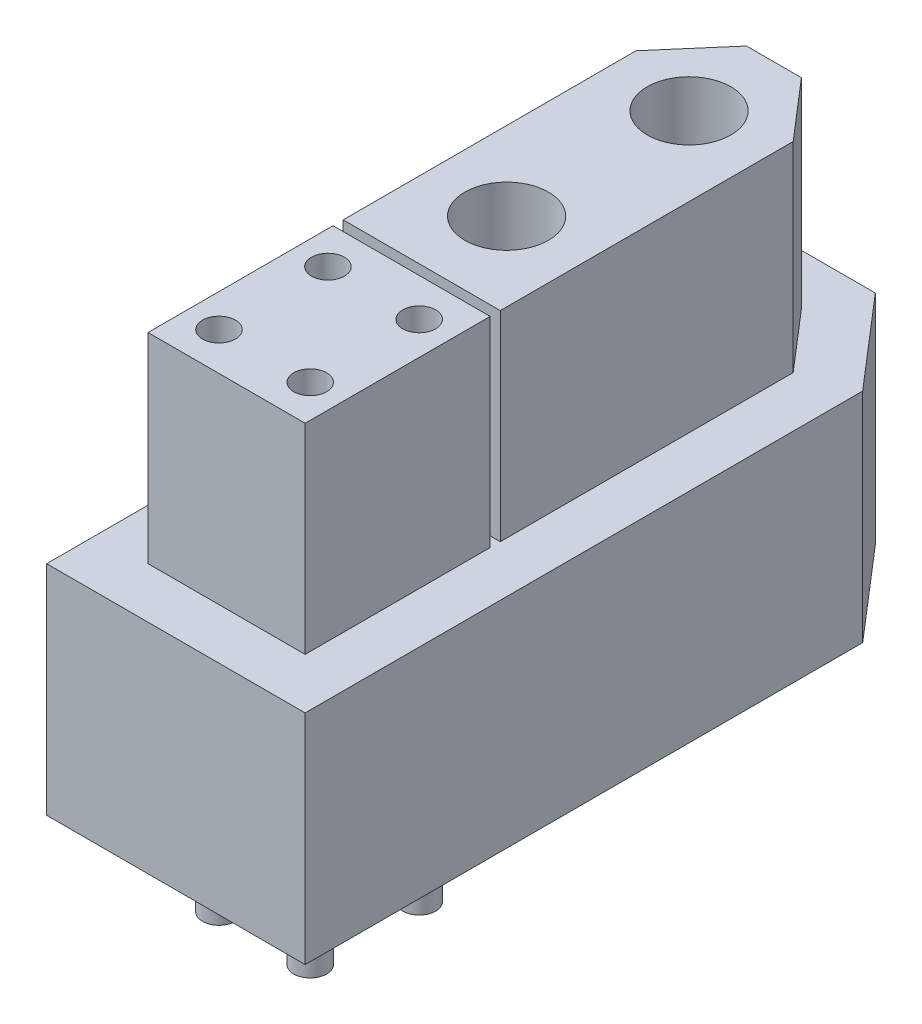
SolidWorks part; units mm, degrees
ref_plane "前视基准面" through (0, 0, 0) normal (0, 0, 1) x (1, 0, 0)
ref_plane "上视基准面" through (0, 0, 0) normal (0, 1, 0) x (1, 0, 0)
ref_plane "右视基准面" through (0, 0, 0) normal (1, 0, 0) x (0, 0, -1)
sketch "草图1" plane through (0, 0, 0) normal (0, 1, 0) x (1, 0, 0)
  line L0 (0, 0) -> (0, 22)
  line L1 (0, 22) -> (3.1, 25.6)
  line L2 (3.1, 25.6) -> (7.1, 25.6)
  line L3 (0, 0) -> (10.2, 0)
  line L4 (5.1, 0) -> (5.1, 25.6) construction
  line L5 (10.2, 22) -> (7.1, 25.6)
  line L6 (10.2, 0) -> (10.2, 22)
  point P3 (2.8038, 20.2062)
  dimension "D1" = 10.2
  dimension "D2" = 25.6
  dimension "D3" = 3.6
  dimension "D4" = 4
extrude "凸台-拉伸1" add sketch "草图1" along normal blind 8.6
sketch "草图2" plane through (0, 8.6, 0) normal (0, 1, 0) x (1, 0, 0)
  line L0 (6.1829, 23.6) -> (6.1829, 9.7) construction
  line L1 (6.1829, 16.65) -> (2.9178, 16.65) construction
  line L2 (8.2, 5.65) -> (2, 5.65) construction
  line L6 (2, 9.7) -> (8.2, 9.7)
  line L7 (2, 9.3) -> (8.2, 9.3)
  line L8 (2, 9.3) -> (2, 2)
  line L9 (8.2, 9.7) -> (8.2, 21.2576)
  line L10 (5.1, 2) -> (5.1, 23.6) construction
  line L12 (2, 2) -> (8.2, 2)
  line L13 (8.2, 2) -> (8.2, 21.2576)
  line L14 (8.2, 21.2576) -> (6.1829, 23.6)
  line L15 (6.1829, 23.6) -> (4.0171, 23.6)
  line L16 (4.0171, 23.6) -> (2, 21.2576)
  line L17 (2, 21.2576) -> (2, 2)
  line L18 (2, 2) -> (8.2, 2)
  line L19 (8.2, 2) -> (8.2, 9.3)
  line L20 (8.2, 21.2576) -> (6.1829, 23.6)
  line L21 (6.1829, 23.6) -> (4.0171, 23.6)
  line L22 (4.0171, 23.6) -> (2, 21.2576)
  line L23 (2, 21.2576) -> (2, 9.7)
  circle A0 centre (5.1, 20.25) radius 1.65
  circle A1 centre (5.1, 13.05) radius 1.65
  circle A2 centre (3.3, 7.8) radius 0.65
  circle A3 centre (6.9, 7.8) radius 0.65
  circle A4 centre (6.9, 3.5) radius 0.65
  circle A5 centre (3.3, 3.5) radius 0.65
  dimension "D4" = 3.3
  dimension "D6" = 1.3
  dimension "D7" = 3.6
  dimension "D2" = 13.9
  dimension "D3" = 7.3
  dimension "D5" = 7.2
  dimension "D8" = 1.5
  dimension "D1" = 2
extrude "凸台-拉伸2" add sketch "草图2" along normal blind 7.9
sketch "草图3" plane through (0, 8.6, 0) normal (0, 1, 0) x (1, 0, 0)
  circle A0 centre (5.1, 20.25) radius 1.65
  circle A1 centre (5.1, 13.05) radius 1.65
  circle A2 centre (3.3, 7.8) radius 0.65
  circle A3 centre (6.9, 7.8) radius 0.65
  circle A4 centre (6.9, 3.5) radius 0.65
  circle A5 centre (3.3, 3.5) radius 0.65
extrude "凸台-拉伸3" add sketch "草图3" against normal blind 12
